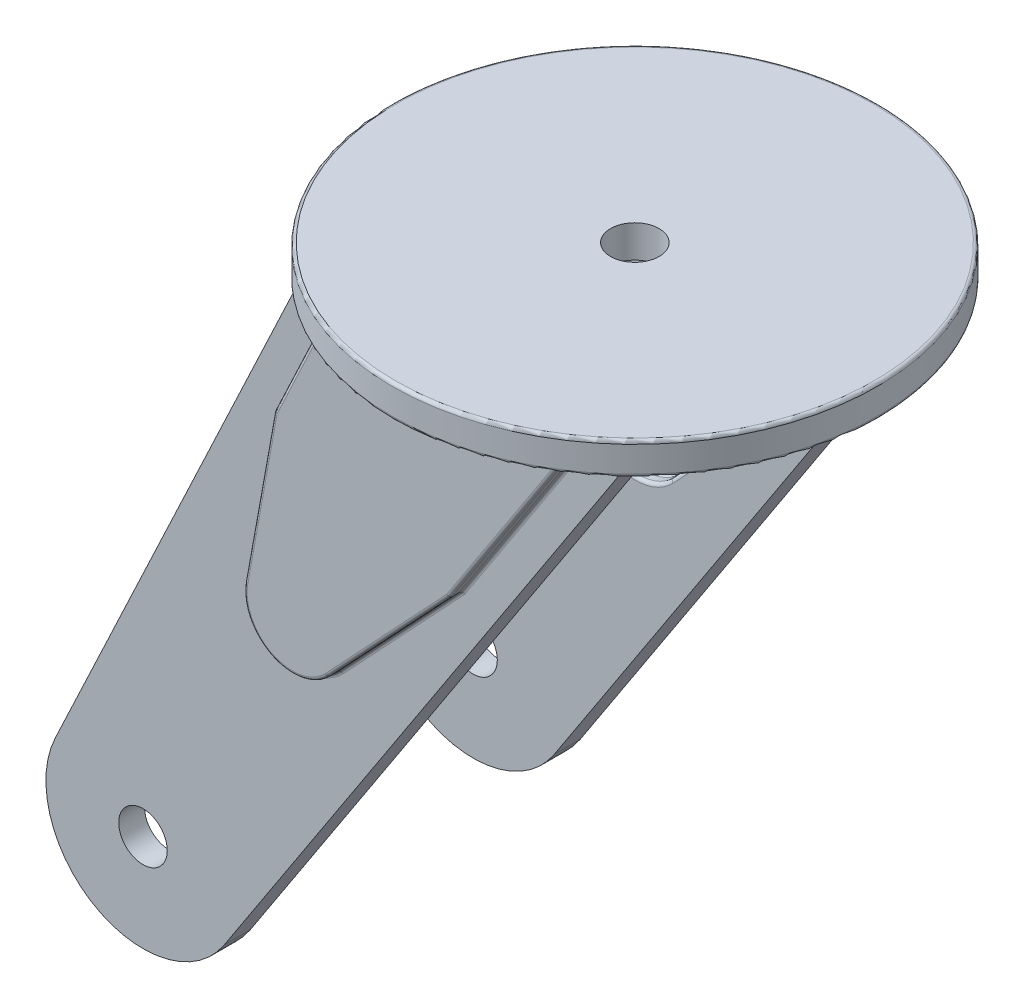
SolidWorks part; units mm, degrees
material "AISI 316 Stainless Steel Sheet (SS)"
ref_plane "Front Plane" through (0, 0, 0) normal (0, 0, 1) x (1, 0, 0)
ref_plane "Top Plane" through (0, 0, 0) normal (0, 1, 0) x (1, 0, 0)
ref_plane "Right Plane" through (0, 0, 0) normal (1, 0, 0) x (0, 0, -1)
sketch "Sketch1" plane through (0, 0, 0) normal (0, 1, 0) x (1, 0, 0)
  circle A0 centre (0, 0) radius 75
  dimension "D1" = 150
extrude "Boss-Extrude1" add sketch "Sketch1" along normal blind 10
fillet "Fillet1" radius 1 2 edges at (0, 0, 75) (0, 10, 75)
ref_plane "Plane1" through (0, 0, 47) normal (0, 0, 1) x (1, 0, 0)
sketch "Sketch2" plane through (0, 0, 47) normal (0, 0, 1) x (1, 0, 0)
  line L0 (0, 0) -> (50, 0)
  line L1 (-74, 0) -> (74, 0) construction
  line L2 (0, 0) -> (-50, 0)
  line L3 (50, 0) -> (-71.8911, -186.4177)
  line L4 (-50, 0) -> (-124.1342, -157.2041)
  arc A0 (-124.1342, -157.2041) -> (-71.8911, -186.4177) centre (-97, -170) ccw
  circle A1 centre (-97, -170) radius 7.5
  dimension "D3" = 60
  dimension "D4" = 170
  dimension "D6" = 15
  dimension "D1" = 50
  dimension "D2" = 50
  dimension "D5" = 147
extrude "Boss-Extrude2" add sketch "Sketch2" along normal blind 8
sketch "Sketch3" plane through (0, 0, 55) normal (0, 0, 1) x (1, 0, 0)
  line L0 (37.5, 0) -> (1.6623, -54.8094)
  line L1 (-49.5076, 0) -> (49.5076, 0) construction
  line L2 (1.6623, -54.8094) -> (-35.8727, -94.8094)
  line L3 (-37.5, 0) -> (-52.5324, -31.8767)
  line L4 (49.5076, 0) -> (-49.5076, 0) construction
  line L5 (-52.5324, -31.8767) -> (-61.5717, -81.8767)
  line L6 (-37.5, 0) -> (37.5, 0)
  line L7 (-50, 0) -> (-124.1342, -157.2041) construction
  line L8 (-71.8911, -186.4177) -> (50, 0) construction
  arc A0 (-61.5717, -81.8767) -> (-35.8727, -94.8094) centre (-46.811, -84.5452) ccw
  dimension "D5" = 15
  dimension "D1" = 75
  dimension "D2" = 37.5
  dimension "D3" = 165
  dimension "D4" = 170
  dimension "D6" = 40
  dimension "D7" = 50
extrude "Boss-Extrude3" add sketch "Sketch3" along normal blind 4
fillet "Fillet2" radius 1 10 edges at (-17.1052, -74.8094, 59) (-53.5539, -97.9442, 59) (-17.1052, -74.8094, 55) (-53.5539, -97.9442, 55) (19.5812, -27.4047, 59) (19.5812, -27.4047, 55) (-45.0162, -15.9383, 55) (-45.0162, -15.9383, 59) (-57.052, -56.8767, 59) (-57.052, -56.8767, 55)
sketch "Sketch4" plane through (0, 0, 47) normal (0, 0, -1) x (-1, 0, 0)
  line L0 (37.5, 0) -> (52.5324, -31.8767) construction
  line L1 (52.5324, -31.8767) -> (61.5717, -81.8767) construction
  line L2 (35.8727, -94.8094) -> (-1.6623, -54.8094) construction
  line L3 (-1.6623, -54.8094) -> (-37.5, 0) construction
  line L4 (37.5, 0) -> (52.5324, -31.8767)
  line L5 (52.5324, -31.8767) -> (61.5717, -81.8767)
  line L6 (35.8727, -94.8094) -> (-1.6623, -54.8094)
  line L7 (-1.6623, -54.8094) -> (-37.5, 0)
  line L8 (-37.5, 0) -> (37.5, 0)
  arc A0 (35.8727, -94.8094) -> (61.5717, -81.8767) centre (46.811, -84.5452) ccw construction
  arc A1 (35.8727, -94.8094) -> (61.5717, -81.8767) centre (46.811, -84.5452) ccw
extrude "Cut-Extrude1" cut sketch "Sketch4" against normal blind 4
fillet "Fillet3" radius 1 10 edges at (-57.052, -56.8767, 47) (-53.5539, -97.9442, 47) (-57.052, -56.8767, 51) (-53.5539, -97.9442, 51) (-45.0162, -15.9383, 47) (-45.0162, -15.9383, 51) (-17.1052, -74.8094, 47) (-17.1052, -74.8094, 51) (19.5812, -27.4047, 47) (19.5812, -27.4047, 51)
mirror "Mirror1" about plane through (0, 0, 0) normal (0, 0, 1) of "Fillet3", "Cut-Extrude1", "Fillet2", "Boss-Extrude3", "Boss-Extrude2"
sketch "Sketch5" plane through (0, 10, 0) normal (0, 1, 0) x (1, 0, 0)
  circle A0 centre (0, 0) radius 7.5
  dimension "D1" = 15
extrude "Cut-Extrude2" cut sketch "Sketch5" against normal through all
scale "Scale1" scale about centroid uniform scaling yes scale factor 0.18
scale "Scale2" scale about centroid uniform scaling yes scale factor 1.04
